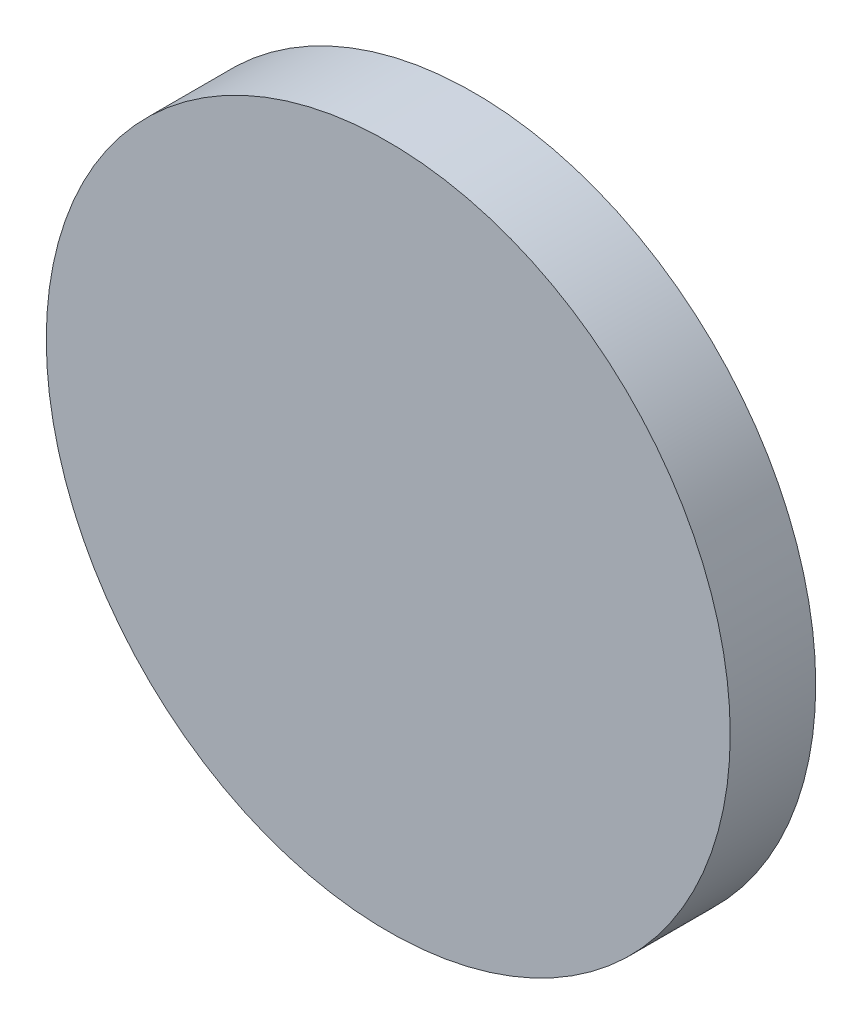
SolidWorks part; units mm, degrees
ref_plane "Front Plane" through (0, 0, 0) normal (0, 0, 1) x (1, 0, 0)
ref_plane "Top Plane" through (0, 0, 0) normal (0, 1, 0) x (1, 0, 0)
ref_plane "Right Plane" through (0, 0, 0) normal (1, 0, 0) x (0, 0, -1)
sketch "Sketch1" plane through (0, 0, 0) normal (0, 0, 1) x (1, 0, 0)
  circle A0 centre (0, 0) radius 14
  dimension "D1" = 28
extrude "Boss-Extrude1" add sketch "Sketch1" along normal blind 3.5
